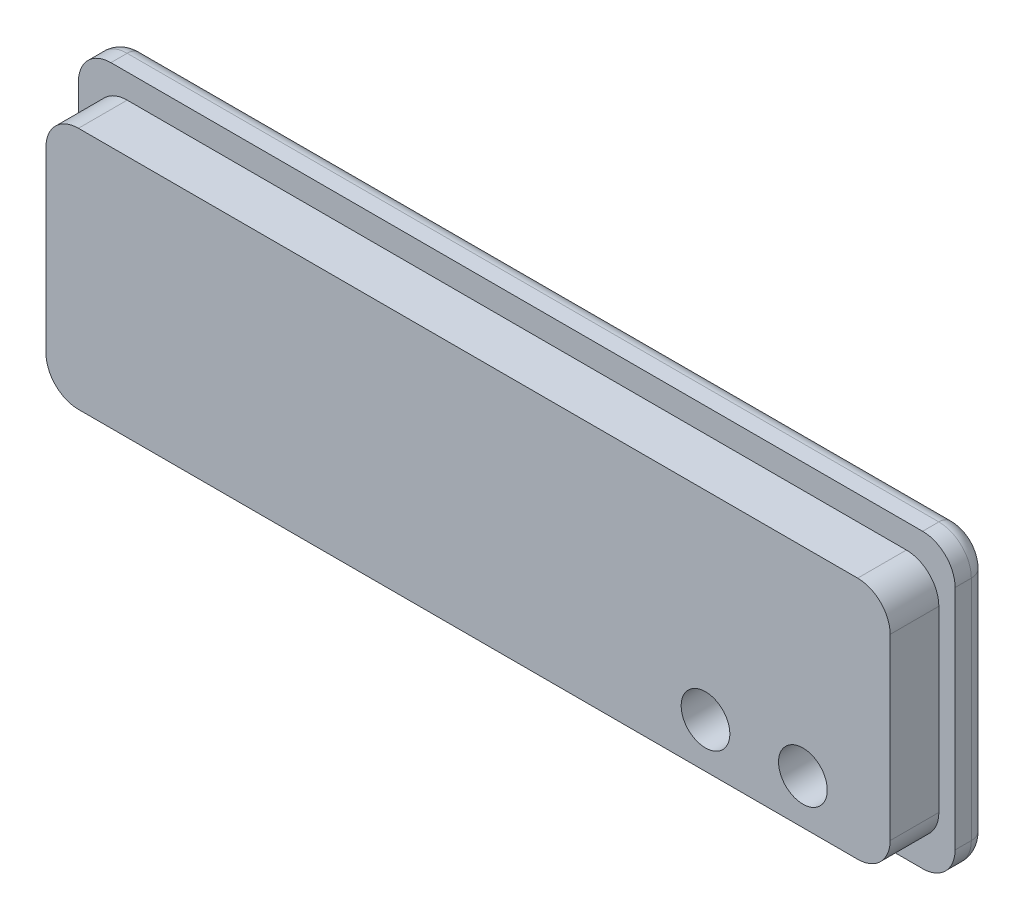
SolidWorks part; units mm, degrees
ref_plane "Front Plane" through (0, 0, 0) normal (0, 0, 1) x (1, 0, 0)
ref_plane "Top Plane" through (0, 0, 0) normal (0, 1, 0) x (1, 0, 0)
ref_plane "Right Plane" through (0, 0, 0) normal (1, 0, 0) x (0, 0, -1)
sketch "Sketch1" plane through (0, 0, 0) normal (0, 0, 1) x (1, 0, 0)
  line L9 (25, 9) -> (-25, 9)
  line L10 (27, 7) -> (27, -7)
  line L11 (25, -9) -> (-25, -9)
  line L12 (-27, 7) -> (-27, -7)
  arc A0 (-27, -7) -> (-25, -9) centre (-25, -7) ccw
  arc A1 (27, -7) -> (25, -9) centre (25, -7) cw
  arc A2 (25, 9) -> (27, 7) centre (25, 7) cw
  arc A3 (-25, 9) -> (-27, 7) centre (-25, 7) ccw
  dimension "D1" = 2
extrude "Boss-Extrude1" add sketch "Sketch1" along normal blind 2
sketch "Sketch2" plane through (0, 0, 2) normal (0, 0, 1) x (1, 0, 0)
  line L1 (24, -7.5) -> (-24, -7.5)
  line L2 (26, -5.5) -> (26, 5.5)
  line L3 (24, 7.5) -> (-24, 7.5)
  line L4 (-26, -5.5) -> (-26, 5.5)
  line L5 (26, -7.5) -> (-26, 7.5) construction
  line L6 (26, 7.5) -> (-26, -7.5) construction
  arc A0 (24, -7.5) -> (26, -5.5) centre (24, -5.5) ccw
  arc A1 (26, 5.5) -> (24, 7.5) centre (24, 5.5) ccw
  arc A2 (-24, -7.5) -> (-26, -5.5) centre (-24, -5.5) cw
  arc A3 (-24, 7.5) -> (-26, 5.5) centre (-24, 5.5) ccw
  point P0 (0, 0)
  dimension "D1" = 2
extrude "Boss-Extrude2" add sketch "Sketch2" along normal blind 3
sketch "Sketch4" plane through (0, 0, 0) normal (0, 0, -1) x (-1, 0, 0)
  circle A0 centre (-20.6256, -4.7453) radius 1.5
  circle A1 centre (-14.6256, -4.7453) radius 1.5
extrude "Cut-Extrude1" cut sketch "Sketch4" against normal blind 7
fillet "Fillet1" radius 1 8 edges at (26.4142, 8.4142, 0) (27, 0, 0) (26.4142, -8.4142, 0) (0, -9, 0) (-26.4142, -8.4142, 0) (-27, 0, 0) (-26.4142, 8.4142, 0) (0, 9, 0)
